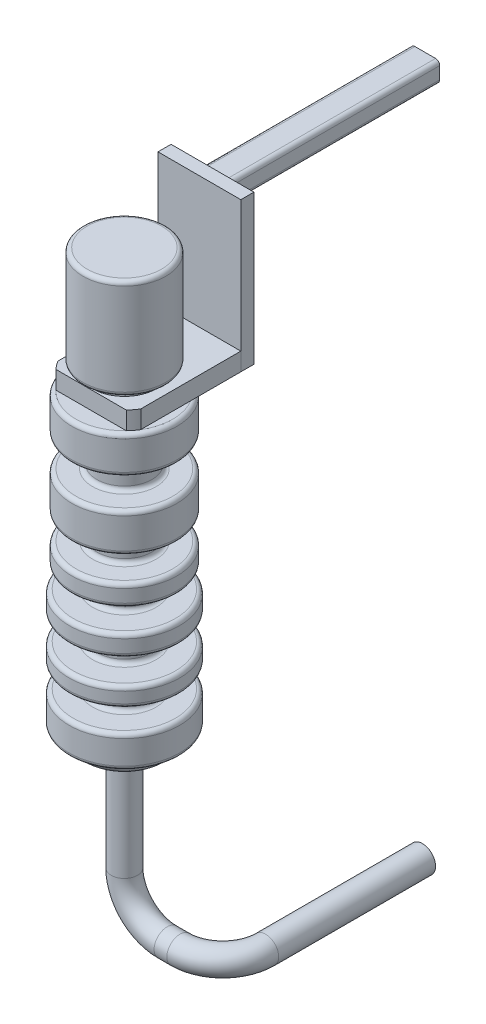
SolidWorks part; units mm, degrees
ref_plane "Alzado" through (0, 0, 0) normal (0, 0, 1) x (1, 0, 0)
ref_plane "Planta" through (0, 0, 0) normal (0, 1, 0) x (1, 0, 0)
ref_plane "Vista lateral" through (0, 0, 0) normal (1, 0, 0) x (0, 0, -1)
sketch "Croquis1" plane through (0, 0, 0) normal (0, 0, 1) x (1, 0, 0)
  line L0 (0, 0) -> (0, 300)
  line L1 (0, 300) -> (27, 300)
  line L2 (35.0571, 161.5537) -> (23, 161.5537)
  line L3 (20, 164.5537) -> (20, 179.8857)
  line L4 (23, 182.8857) -> (35.0571, 182.8857)
  line L5 (38.0571, 185.8857) -> (38.0571, 206.895)
  line L6 (38.0571, 158.5537) -> (38.0571, 136.5938)
  line L7 (35.0571, 133.5938) -> (23, 133.5938)
  line L8 (20, 130.5938) -> (20, 119.0378)
  line L9 (23, 116.0378) -> (35.0571, 116.0378)
  line L10 (38.0571, 113.0378) -> (38.0571, 103.7977)
  line L11 (35.0571, 100.7977) -> (23, 100.7977)
  line L12 (20, 97.7977) -> (20, 88.8577)
  line L13 (23, 85.8577) -> (37, 85.8577)
  line L14 (40, 82.8577) -> (40, 73.6852)
  line L15 (37, 0) -> (0, 0)
  line L16 (35.0571, 209.895) -> (23, 209.895)
  line L17 (20, 212.895) -> (20, 224.451)
  line L18 (23, 227.451) -> (27, 227.451)
  line L19 (30, 230.451) -> (30, 297)
  line L20 (37, 70.6852) -> (23, 70.6852)
  line L21 (20, 67.6852) -> (20, 55.9894)
  line L22 (23, 52.9894) -> (37, 52.9894)
  line L23 (40, 49.9894) -> (40, 42.0856)
  line L24 (37, 39.0856) -> (23, 39.0856)
  line L25 (20, 36.0856) -> (20, 26.2859)
  line L26 (23, 23.2859) -> (37, 23.2859)
  line L27 (40, 20.2859) -> (40, 3)
  arc A0 (30, 297) -> (27, 300) centre (27, 297) ccw
  arc A1 (27, 227.451) -> (30, 230.451) centre (27, 230.451) ccw
  arc A2 (20, 224.451) -> (23, 227.451) centre (23, 224.451) cw
  arc A3 (23, 209.895) -> (20, 212.895) centre (23, 212.895) cw
  arc A4 (38.0571, 206.895) -> (35.0571, 209.895) centre (35.0571, 206.895) ccw
  arc A5 (20, 179.8857) -> (23, 182.8857) centre (23, 179.8857) cw
  arc A6 (23, 161.5537) -> (20, 164.5537) centre (23, 164.5537) cw
  arc A7 (35.0571, 161.5537) -> (38.0571, 158.5537) centre (35.0571, 158.5537) cw
  arc A8 (35.0571, 182.8857) -> (38.0571, 185.8857) centre (35.0571, 185.8857) ccw
  arc A9 (40, 3) -> (37, 0) centre (37, 3) cw
  arc A10 (20, 26.2859) -> (23, 23.2859) centre (23, 26.2859) ccw
  arc A11 (23, 39.0856) -> (20, 36.0856) centre (23, 36.0856) ccw
  arc A12 (20, 55.9894) -> (23, 52.9894) centre (23, 55.9894) ccw
  arc A13 (23, 70.6852) -> (20, 67.6852) centre (23, 67.6852) ccw
  arc A14 (20, 88.8577) -> (23, 85.8577) centre (23, 88.8577) ccw
  arc A15 (23, 100.7977) -> (20, 97.7977) centre (23, 97.7977) ccw
  arc A16 (20, 119.0378) -> (23, 116.0378) centre (23, 119.0378) ccw
  arc A17 (23, 133.5938) -> (20, 130.5938) centre (23, 130.5938) ccw
  arc A18 (38.0571, 136.5938) -> (35.0571, 133.5938) centre (35.0571, 136.5938) cw
  arc A19 (35.0571, 116.0378) -> (38.0571, 113.0378) centre (35.0571, 113.0378) cw
  arc A20 (38.0571, 103.7977) -> (35.0571, 100.7977) centre (35.0571, 103.7977) cw
  arc A21 (37, 85.8577) -> (40, 82.8577) centre (37, 82.8577) cw
  arc A22 (40, 73.6852) -> (37, 70.6852) centre (37, 73.6852) cw
  arc A23 (37, 52.9894) -> (40, 49.9894) centre (37, 49.9894) cw
  arc A24 (40, 42.0856) -> (37, 39.0856) centre (37, 42.0856) cw
  arc A25 (37, 23.2859) -> (40, 20.2859) centre (37, 20.2859) cw
  dimension "D2" = 3
  dimension "D1" = 300
revolve "Revolución2" add sketch "Croquis1" angle 360 about L0
sketch "Croquis2" plane through (0, 0, 0) normal (0, -1, 0) x (1, 0, 0)
  circle A0 centre (0, 0) radius 29.7333
extrude "Saliente-Extruir1" add sketch "Croquis2" along normal blind 10
fillet "Redondeo1" radius 5 1 edges at (0, -10, -29.7333)
sketch "Croquis3" plane through (0, 209.895, 0) normal (0, 1, 0) x (1, 0, 0)
  line L0 (30, -24.0833) -> (-30, -24.0833)
  line L2 (30, -24.0833) -> (30, 54.3419)
  line L3 (30, 54.3419) -> (-30, 54.3419)
  line L4 (-30, -24.0833) -> (-30, 54.3419)
  line L5 (13.2954, -24.0833) -> (-30, 54.3419) construction
  line L6 (30, 54.3419) -> (-13.2954, -24.0833) construction
  circle A0 centre (0, 0) radius 27
  point P0 (0, 0)
  circle M2 centre (0, 0) radius 23
  circle M3 centre (0, 0) radius 35.0571
  dimension "D1" = 60
extrude "Saliente-Extruir2" add sketch "Croquis3" along normal blind 13 contours L4 L2 L3 M3 | A0 L0 L2 L4 M3 | L0 A0 M2
sketch "Croquis4" plane through (0, 209.895, 0) normal (0, -1, 0) x (1, 0, 0)
  line L0 (30, -54.3419) -> (30, -63.813)
  line L1 (30, -63.813) -> (-29.0961, -63.813)
  line L2 (-30, -54.3419) -> (-30, -63.813)
  line L3 (-30, -63.813) -> (-29.0961, -63.813)
  line L4 (-30, -54.3419) -> (30, -54.3419)
extrude "Saliente-Extruir3" add sketch "Croquis4" against normal blind 108 separate body
sketch "Croquis5" plane through (0, 0, -63.813) normal (0, 0, -1) x (-1, 0, 0)
  line L1 (-7.5749, 298.627) -> (7.315, 298.627)
  line L2 (-10.5749, 301.627) -> (-10.5749, 310.5358)
  line L3 (-7.5749, 313.5358) -> (7.315, 313.5358)
  line L4 (10.315, 301.627) -> (10.315, 310.5358)
  line L5 (-10.5749, 298.627) -> (10.315, 313.5358) construction
  line L6 (-10.5749, 313.5358) -> (10.315, 298.627) construction
  arc A0 (-10.5749, 310.5358) -> (-7.5749, 313.5358) centre (-7.5749, 310.5358) cw
  arc A1 (-7.5749, 298.627) -> (-10.5749, 301.627) centre (-7.5749, 301.627) cw
  arc A2 (7.315, 298.627) -> (10.315, 301.627) centre (7.315, 301.627) ccw
  arc A3 (7.315, 313.5358) -> (10.315, 310.5358) centre (7.315, 310.5358) cw
  point P0 (-0.1299, 306.0814)
  dimension "D1" = 3
extrude "Saliente-Extruir4" add sketch "Croquis5" along normal blind 154
sketch3d "Croquis3D2"
  line L0 (0, 0, 0) -> (0, -89, 0)
  line L1 (31, -120, 0) -> (40.2629, -120, 0)
  line L2 (71.2629, -120, -31) -> (71.2629, -120, -144.6254)
  arc A0 (40.2629, -120, 0) -> (71.2629, -120, -31) centre (40.2629, -120, -31) ccw
  arc A1 (0, -89, 0) -> (31, -120, 0) centre (31, -89, 0) ccw
  point P7 (71.2629, -120, 0)
  point P8 (40.2629, -89, -31)
  point P11 (0, -120, 0)
  point P12 (31, -89, 31)
  dimension "D1" = 31
  dimension "D2" = 120
sweep "Barrer2" add path "Croquis3D2" circular profile diameter 19 parameters "D3"=19
